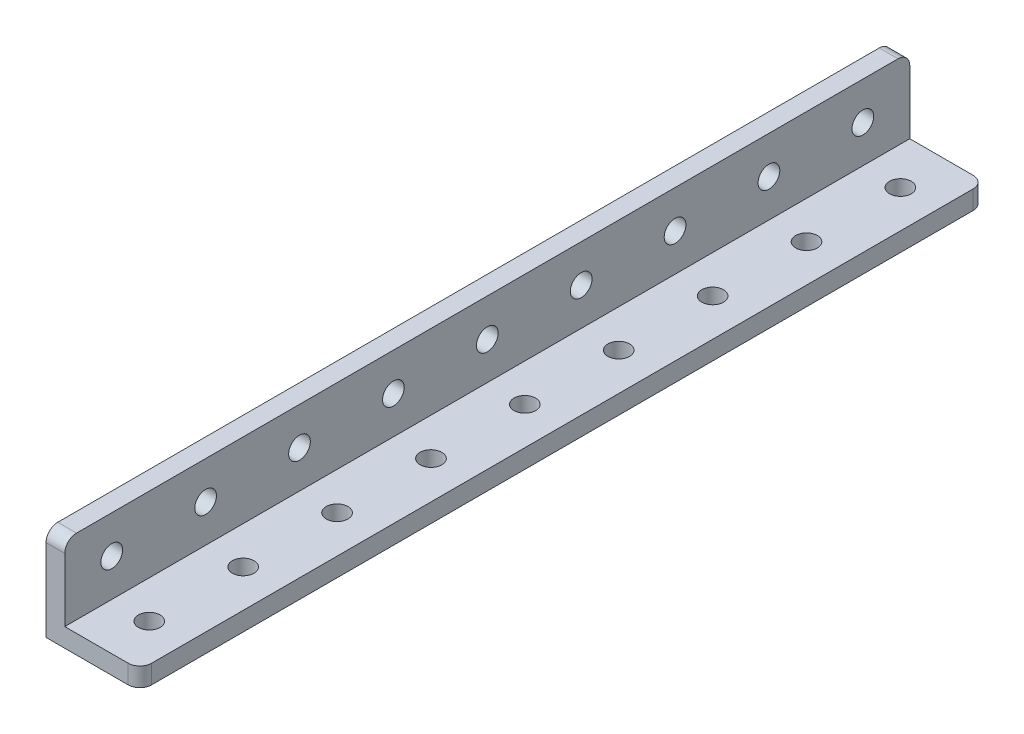
SolidWorks part; units mm, degrees
material "5052 Alloy"
ref_plane "Front Plane" through (0, 0, 0) normal (0, 0, 1) x (1, 0, 0)
ref_plane "Top Plane" through (0, 0, 0) normal (0, 1, 0) x (1, 0, 0)
ref_plane "Right Plane" through (0, 0, 0) normal (1, 0, 0) x (0, 0, -1)
sketch "Sketch1" plane through (0, 0, 0) normal (0, 0, 1) x (1, 0, 0)
  line L0 (0, 0) -> (16, 0)
  line L1 (16, 0) -> (16, 3.2)
  line L2 (16, 3.2) -> (3.2, 3.2)
  line L3 (3.2, 3.2) -> (3.2, 16)
  line L4 (3.2, 16) -> (0, 16)
  line L5 (0, 16) -> (0, 0)
  dimension "D1" = 16
  dimension "D2" = 3.2
  dimension "D3" = 16
  dimension "D4" = 3.2
extrude "Extrude1" add sketch "Sketch1" against normal mid plane 144
fillet "Fillet1" radius 2 4 edges at (1.6, 16, 72) (1.6, 16, -72) (16, 1.6, -72) (16, 1.6, 72)
sketch "Sketch2" plane through (0, 0, 0) normal (-1, 0, 0) x (0, 0, 1)
  line L0 (-72, 0) -> (72, 0) construction
  circle A0 centre (0, 9.6) radius 1.85
  dimension "D1" = 3.7
  dimension "D2" = 9.6
extrude "Cut-Extrude1" cut sketch "Sketch2" against normal through all
sketch "Sketch3" plane through (0, 0, 0) normal (0, -1, 0) x (1, 0, 0)
  line L3 (0, -70) -> (0, 70) construction
  circle A0 centre (9.6, 0) radius 1.85
  dimension "D1" = 3.7
  dimension "D2" = 9.6
extrude "Cut-Extrude2" cut sketch "Sketch3" against normal through all
pattern_linear "LPattern1" count 5 spacing 16 along (0, 0, 1) count 5 spacing 16 along (0, 0, -1) of "Cut-Extrude1", "Cut-Extrude2"
